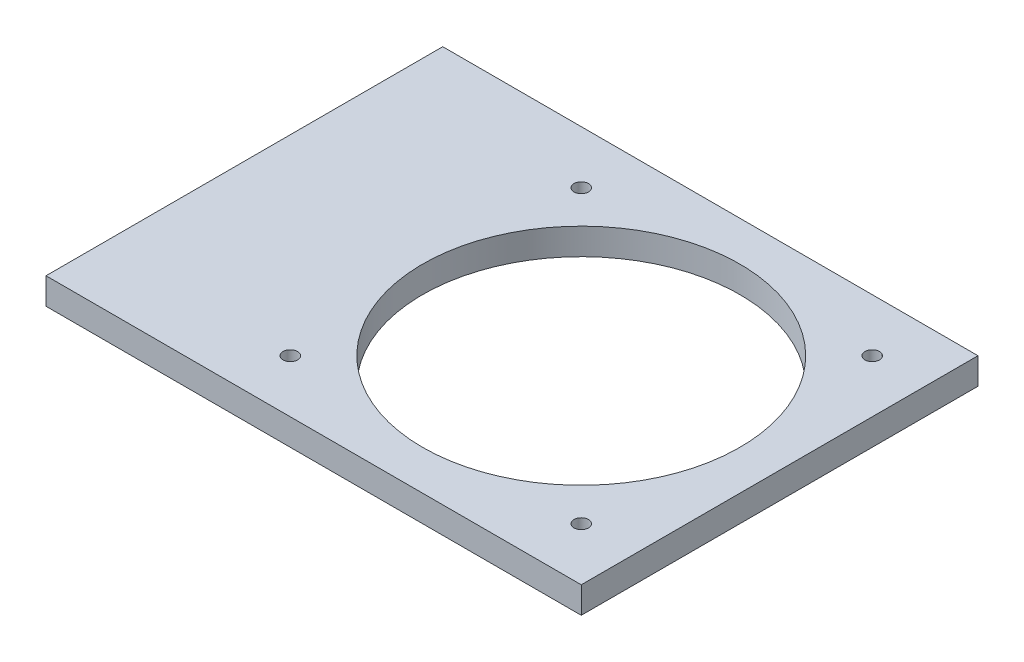
SolidWorks part; units mm, degrees
ref_plane "Front Plane" through (0, 0, 0) normal (0, 0, 1) x (1, 0, 0)
ref_plane "Top Plane" through (0, 0, 0) normal (0, 1, 0) x (1, 0, 0)
ref_plane "Right Plane" through (0, 0, 0) normal (1, 0, 0) x (0, 0, -1)
sketch "Sketch4" plane through (0, 0, 0) normal (0, 0, 1) x (1, 0, 0)
  line L0 (0, 0) -> (36.6665, 419.1) construction
  line L1 (36.6665, 419.1) -> (155.7226, 419.1) construction
  line L2 (155.7226, 419.1) -> (155.7226, 0) construction
  line L3 (155.7226, 0) -> (0, 0) construction
  line L4 (155.7226, -1000) -> (155.7226, 49000) construction
  line L5 (1.8042, 20.6221) -> (36.6665, 419.1) construction
  line L6 (1.8042, 20.6221) -> (41.652, 17.1359) construction
  line L7 (36.6665, 419.1) -> (76.5143, 415.6138) construction
  line L8 (41.652, 17.1359) -> (76.5143, 415.6138) construction
  line L9 (60.4726, -1000) -> (60.4726, 49000) construction
  line L10 (-52.7184, 317.5) -> (-128.6284, 324.1413) construction
  line L11 (-30.1965, 414.3375) -> (36.6601, 414.3375) construction
  line L12 (-1162.1335, 304.8) -> (48837.8665, 304.8) construction
  line L13 (-130.0274, 292.1) -> (-53.8274, 292.1) construction
  line L14 (-128.6284, 324.1413) -> (-53.8274, 292.1) construction
  line L15 (-52.7184, 317.5) -> (-130.0274, 292.1) construction
  line L16 (36.6601, 338.1375) -> (-30.1965, 338.1375) construction
  line L17 (-138.1172, 324.9714) -> (27.1662, 310.511)
  line L18 (-138.1172, 324.9714) -> (-137.5638, 331.2973)
  line L19 (-137.5638, 331.2973) -> (36.6665, 419.1)
  line L20 (36.6665, 419.1) -> (104.9226, 419.1)
  line L21 (104.9226, 419.1) -> (104.9226, 0) construction
  line L22 (27.1662, 310.511) -> (0.3389, 3.8741)
  line L23 (0.3389, 3.8741) -> (44.6198, 0)
  line L24 (44.6198, 0) -> (104.9226, 0)
  line L25 (104.9226, 419.1) -> (155.7226, 311.15)
  line L26 (155.7226, 311.15) -> (155.7226, 304.8)
  line L27 (155.7226, 304.8) -> (104.9226, 280.8941)
  line L28 (104.9226, 280.8941) -> (104.9226, 0)
  arc A0 (-128.6284, 324.1413) -> (-30.1965, 414.3375) centre (-30.1965, 315.5296) cw construction
  arc A1 (69.9976, 304.8) -> (36.6601, 338.1375) centre (36.6601, 304.8) ccw construction
  arc A2 (146.1976, 304.8) -> (36.6601, 414.3375) centre (36.6601, 304.8) ccw construction
  arc A3 (-52.7184, 317.5) -> (-30.1965, 338.1375) centre (-30.1965, 315.5296) cw construction
  point P7 (54.1226, 400.05)
  point P17 (146.1976, 304.8)
  point P18 (69.9976, 304.8)
  dimension "D9" = 9.525
  dimension "D14" = 25.4
  dimension "D1" = 419.1
  dimension "D2" = 101.6
  dimension "D3" = 19.05
  dimension "D4" = 19.05
  dimension "D5" = 85
  dimension "D6" = 40
  dimension "D7" = 400
  dimension "D8" = 95.25
  dimension "D10" = 9.525
  dimension "D11" = 114.3
  dimension "D12" = 76.2
  dimension "D13" = 9.525
  dimension "D15" = 127
  dimension "D16" = 9.525
  dimension "D17" = 209.55
  dimension "D18" = 6.35
  dimension "D19" = 50.8
  dimension "D20" = 44.45
  dimension "D21" = 6.35
sketch "Sketch5" plane through (0, 0, 0) normal (0, 0, 1) x (1, 0, 0)
  line L0 (0, 0) -> (36.6665, 419.1) construction
  line L1 (155.7226, 304.8) -> (27.2221, 304.8)
  line L2 (155.7226, 304.8) -> (155.7226, 311.15)
  line L3 (155.7226, 311.15) -> (27.2221, 311.15)
  line L4 (27.2221, 304.8) -> (27.2221, 311.15)
extrude "Boss-Extrude1" add sketch "Sketch5" along normal blind 95.25
sketch "Sketch6" plane through (0, 311.15, 0) normal (0, 1, 0) x (1, 0, 0)
  line L0 (155.7226, -47.625) -> (108.0976, -47.625) construction
  line L1 (155.7226, -95.25) -> (155.7226, 0) construction
  line L3 (143.0226, -82.55) -> (73.1726, -82.55) construction
  line L4 (143.0226, -82.55) -> (143.0226, -12.7) construction
  line L5 (143.0226, -12.7) -> (73.1726, -12.7) construction
  line L6 (73.1726, -82.55) -> (73.1726, -12.7) construction
  line L7 (143.0226, -82.55) -> (73.1726, -12.7) construction
  line L8 (143.0226, -12.7) -> (73.1726, -82.55) construction
  circle A0 centre (108.0976, -47.625) radius 38.1
  circle A1 centre (73.1726, -12.7) radius 1.75
  circle A2 centre (73.1726, -82.55) radius 1.75
  circle A3 centre (143.0226, -82.55) radius 1.75
  circle A4 centre (143.0226, -12.7) radius 1.75
  dimension "D1" = 76.2
  dimension "D4" = 3.5
  dimension "D2" = 47.625
  dimension "D3" = 69.85
extrude "Cut-Extrude3" cut sketch "Sketch6" against normal through all
